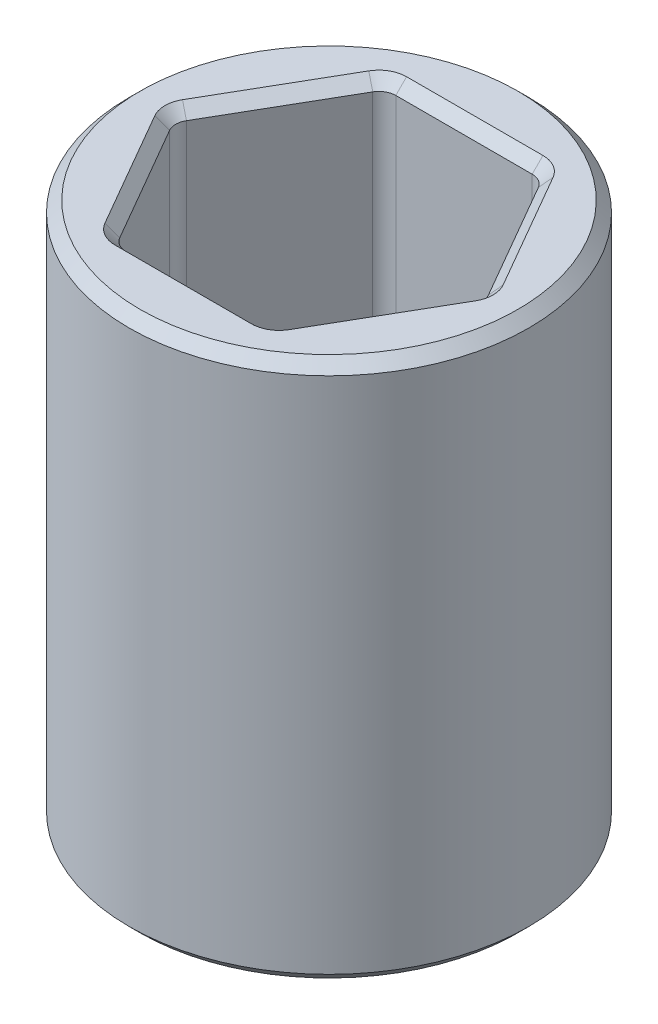
SolidWorks part; units mm, degrees
ref_plane "Front" through (0, 0, 0) normal (0, 0, 1) x (1, 0, 0)
ref_plane "Top" through (0, 0, 0) normal (0, 1, 0) x (1, 0, 0)
ref_plane "Right" through (0, 0, 0) normal (1, 0, 0) x (0, 0, -1)
sketch "Sketch4" plane through (0, 0, 0) normal (0, 1, 0) x (1, 0, 0)
  circle A0 centre (0, 0) radius 4.699
  circle A1 centre (0, 0) radius 1.5875
  dimension "D1" = 9.398
  dimension "D2" = 3.175
extrude "Boss-Extrude1" add sketch "Sketch4" along normal blind 12.7
sketch "Sketch7" plane through (0, 0, 0) normal (0, -1, 0) x (1, 0, 0)
  line L1 (1.6498, 2.8575) -> (-1.6498, 2.8575)
  line L2 (-1.6498, 2.8575) -> (-3.2996, 0)
  line L3 (-3.2996, 0) -> (-1.6498, -2.8575)
  line L4 (-1.6498, -2.8575) -> (1.6498, -2.8575)
  line L5 (1.6498, -2.8575) -> (3.2996, 0)
  line L6 (3.2996, 0) -> (1.6498, 2.8575)
  circle A0 centre (0, 0) radius 2.8575 construction
  dimension "D1" = 5.715
extrude "Cut-Extrude3" cut sketch "Sketch7" against normal blind 3.175
ref_plane "Plane1" through (0, 6.35, 0) normal (0, -1, 0) x (-1, 0, 0)
sketch "Sketch6" plane through (0, 12.7, 0) normal (0, 1, 0) x (1, 0, 0)
  line L1 (1.8331, 3.175) -> (-1.8331, 3.175)
  line L2 (-1.8331, 3.175) -> (-3.6662, 0)
  line L3 (-3.6662, 0) -> (-1.8331, -3.175)
  line L4 (-1.8331, -3.175) -> (1.8331, -3.175)
  line L5 (1.8331, -3.175) -> (3.6662, 0)
  line L6 (3.6662, 0) -> (1.8331, 3.175)
  circle A0 centre (0, 0) radius 3.175 construction
  dimension "D1" = 6.35
extrude "Cut-Extrude2" cut sketch "Sketch6" against normal up to surface (6.35 mm away)
fillet "Fillet1-1/64" radius 0.3969 24 edges at (-2.7496, 6.35, 1.5875) (0, 6.35, 3.175) (2.7496, 6.35, 1.5875) (2.7496, 6.35, -1.5875) (0, 6.35, -3.175) (-2.7496, 6.35, -1.5875) (-3.6662, 9.525, 0) (-1.8331, 9.525, 3.175) (1.8331, 9.525, 3.175) (3.6662, 9.525, 0) (1.8331, 9.525, -3.175) (-1.8331, 9.525, -3.175) (0, 3.175, 2.8575) (-2.4747, 3.175, 1.4287) (-2.4747, 3.175, -1.4288) (0, 3.175, -2.8575) (2.4747, 3.175, -1.4287) (2.4747, 3.175, 1.4288) (-1.6498, 1.5875, 2.8575) (-3.2996, 1.5875, 0) (-1.6498, 1.5875, -2.8575) (1.6498, 1.5875, -2.8575) (3.2996, 1.5875, 0) (1.6498, 1.5875, 2.8575)
chamfer "Chamfer1" distance 0.254 angle 45 28 edges at (0, 6.35, -1.5875) (-2.7496, 12.7, -1.5875) (-3.6048, 12.7, 0) (-1.8024, 12.7, -3.1218) (-2.7496, 12.7, 1.5875) (0, 12.7, -3.175) (-1.8024, 12.7, 3.1218) (1.8024, 12.7, -3.1218) (0, 12.7, 3.175) (2.7496, 12.7, -1.5875) (1.8024, 12.7, 3.1218) (3.6048, 12.7, 0) (2.7496, 12.7, 1.5875) (0, 12.7, 4.699) (0, 3.175, -1.5875) (-2.4747, 0, -1.4288) (-1.6191, 0, -2.8043) (-3.2382, 0, 0) (0, 0, -2.8575) (-2.4747, 0, 1.4287) (1.6191, 0, -2.8043) (-1.6191, 0, 2.8043) (2.4747, 0, -1.4287) (0, 0, 2.8575) (3.2382, 0, 0) (1.6191, 0, 2.8043) (2.4747, 0, 1.4288) (0, 0, 4.699)
